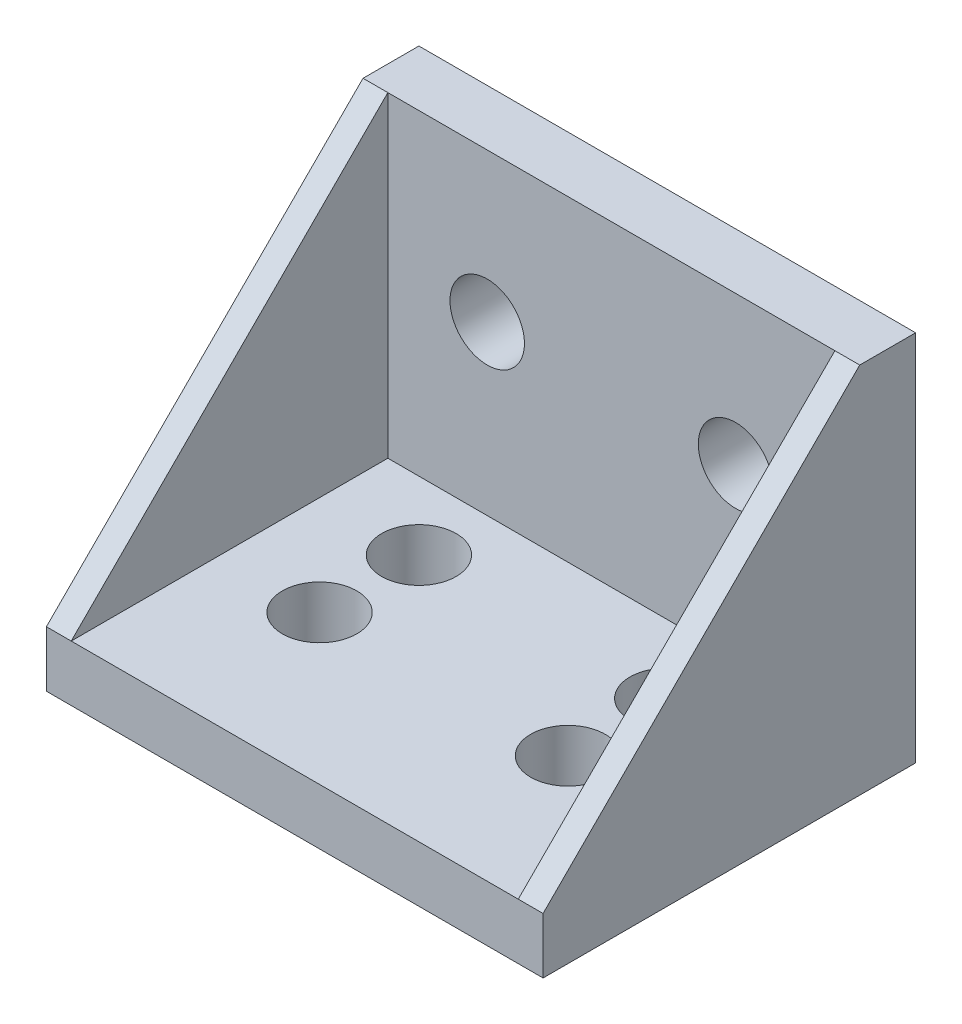
SolidWorks part; units mm, degrees
ref_plane "Front Plane" through (0, 0, 0) normal (0, 0, 1) x (1, 0, 0)
ref_plane "Top Plane" through (0, 0, 0) normal (0, 1, 0) x (1, 0, 0)
ref_plane "Right Plane" through (0, 0, 0) normal (1, 0, 0) x (0, 0, -1)
sketch "Sketch1" plane through (0, 0, 0) normal (1, 0, 0) x (0, 0, -1)
  line L0 (0, 0) -> (0, 30)
  line L1 (0, 30) -> (-4.5, 30)
  line L2 (-4.5, 30) -> (-4.5, 4.5)
  line L3 (-4.5, 4.5) -> (-30, 4.5)
  line L4 (-30, 4.5) -> (-30, 0)
  line L5 (-30, 0) -> (0, 0)
  dimension "D1" = 4.5
  dimension "D2" = 4.5
  dimension "D3" = 30
  dimension "D4" = 30
extrude "Boss-Extrude1" add sketch "Sketch1" along normal mid plane 40
sketch "Sketch2" plane through (0, 0, 4.5) normal (0, 0, 1) x (1, 0, 0)
  line L0 (-20, 18) -> (20, 18) construction
  line L1 (-20, 30) -> (-20, 4.5) construction
  line L2 (20, 30) -> (20, 4.5) construction
  line L3 (20, 0) -> (-20, 0) construction
  circle A0 centre (-10, 18) radius 3
  circle A1 centre (10, 18) radius 3
  dimension "D1" = 20
  dimension "D2" = 10
  dimension "D3" = 6
  dimension "D4" = 18
extrude "Cut-Extrude1" cut sketch "Sketch2" against normal through all
sketch "Sketch3" plane through (0, 4.5, 0) normal (0, 1, 0) x (1, 0, 0)
  line L0 (-20, -10) -> (20, -10) construction
  line L1 (-20, -4.5) -> (-20, -30) construction
  line L2 (20, -4.5) -> (20, -30) construction
  line L3 (20, -18) -> (-20, -18) construction
  line L4 (-10, -10) -> (-10, -18) construction
  line L5 (10, -10) -> (10, -18) construction
  line L6 (20, 0) -> (-20, 0) construction
  circle A0 centre (-10, -10) radius 3
  circle A1 centre (-10, -18) radius 3
  circle A2 centre (10, -10) radius 3
  circle A3 centre (10, -18) radius 3
  dimension "D1" = 6
  dimension "D4" = 20
  dimension "D5" = 10
  dimension "D2" = 10
  dimension "D3" = 18
extrude "Cut-Extrude2" cut sketch "Sketch3" against normal through all
sketch "Sketch4" plane through (20, 0, 0) normal (1, 0, 0) x (0, 0, -1)
  line L0 (0, 0) -> (0, 30) construction
  line L1 (-30, 0) -> (0, 0) construction
  line L2 (0, 30) -> (-4.5, 30) construction
  line L3 (-30, 4.5) -> (-30, 0) construction
  line L4 (0, 0) -> (0, 30)
  line L5 (-30, 0) -> (0, 0)
  line L6 (0, 30) -> (-4.5, 30)
  line L7 (-30, 4.5) -> (-30, 0)
  line L8 (-4.5, 30) -> (-30, 4.5)
extrude "Boss-Extrude2" add sketch "Sketch4" against normal blind 2
sketch "Sketch5" plane through (-20, 0, 0) normal (-1, 0, 0) x (0, 0, 1)
  line L3 (30, 4.5) -> (4.5, 30)
  line L4 (4.5, 30) -> (4.5, 4.5)
  line L5 (4.5, 4.5) -> (30, 4.5)
  line L6 (30, 4.5) -> (4.5, 30)
  line L7 (4.5, 30) -> (4.5, 4.5)
  line L8 (4.5, 4.5) -> (30, 4.5)
  dimension "D1" = 0
extrude "Boss-Extrude3" add sketch "Sketch5" against normal blind 2
